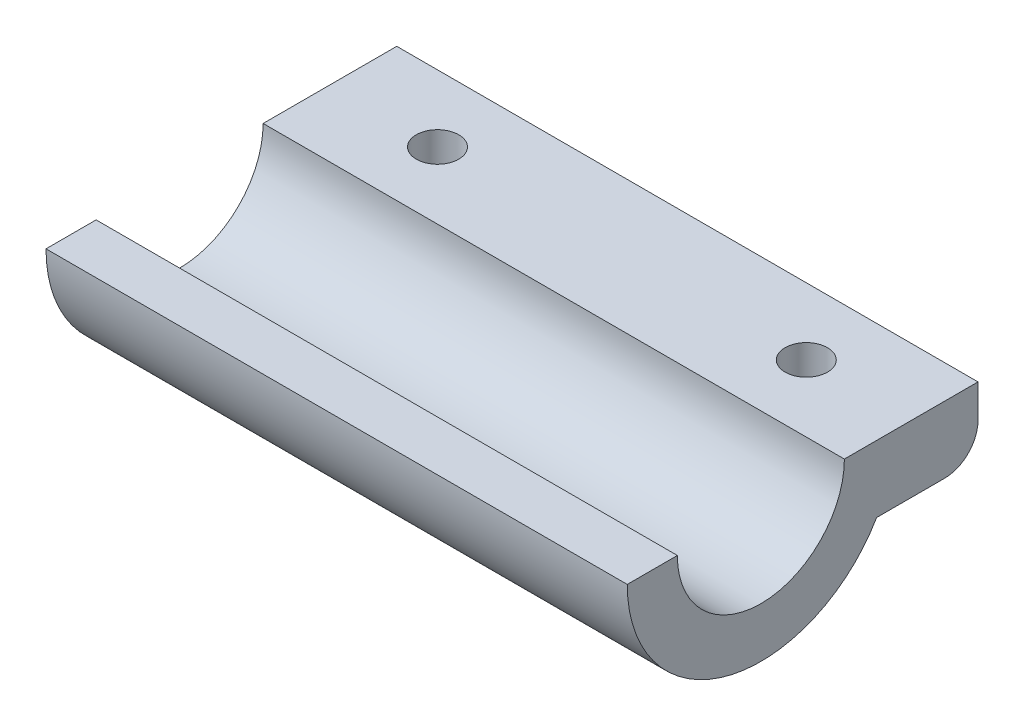
SolidWorks part; units mm, degrees
ref_plane "Front Plane" through (0, 0, 0) normal (0, 0, 1) x (1, 0, 0)
ref_plane "Top Plane" through (0, 0, 0) normal (0, 1, 0) x (1, 0, 0)
ref_plane "Right Plane" through (0, 0, 0) normal (1, 0, 0) x (0, 0, -1)
sketch "Sketch1" plane through (0, 0, 0) normal (1, 0, 0) x (0, 0, -1)
  line L0 (-32.5, 0) -> (-25, 0)
  line L1 (0, 0) -> (7.5, 0)
  line L3 (0, 0) -> (20, 0)
  line L5 (4.8205, -10) -> (20, -10)
  line L6 (20, 0) -> (20, -10)
  arc A0 (-25, 0) -> (0, 0) centre (-12.5, 0) ccw
  arc A1 (-32.5, 0) -> (4.8205, -10) centre (-12.5, 0) ccw
  dimension "D1" = 25
  dimension "D2" = 40
  dimension "D3" = 20
  dimension "D4" = 10
extrude "Boss-Extrude1" add sketch "Sketch1" along normal blind 87 contours L3 L6 L5 A1 L0 A0
sketch "Sketch2" plane through (0, 0, 0) normal (0, 1, 0) x (1, 0, 0)
  line L0 (0, 0) -> (0, 20) construction
  line L1 (87, 0) -> (87, 20) construction
  line L2 (87, 20) -> (0, 20) construction
  circle A0 centre (16.1, 10) radius 3.175
  circle A1 centre (71.3, 10) radius 3.175
  dimension "D1" = 6.35
  dimension "D2" = 6.35
  dimension "D3" = 16.1
  dimension "D4" = 15.7
  dimension "D5" = 10
extrude "Cut-Extrude1" cut sketch "Sketch2" against normal through all contours A1 | A0
fillet "Fillet1" radius 5 1 edges at (43.5, -10, -20)
